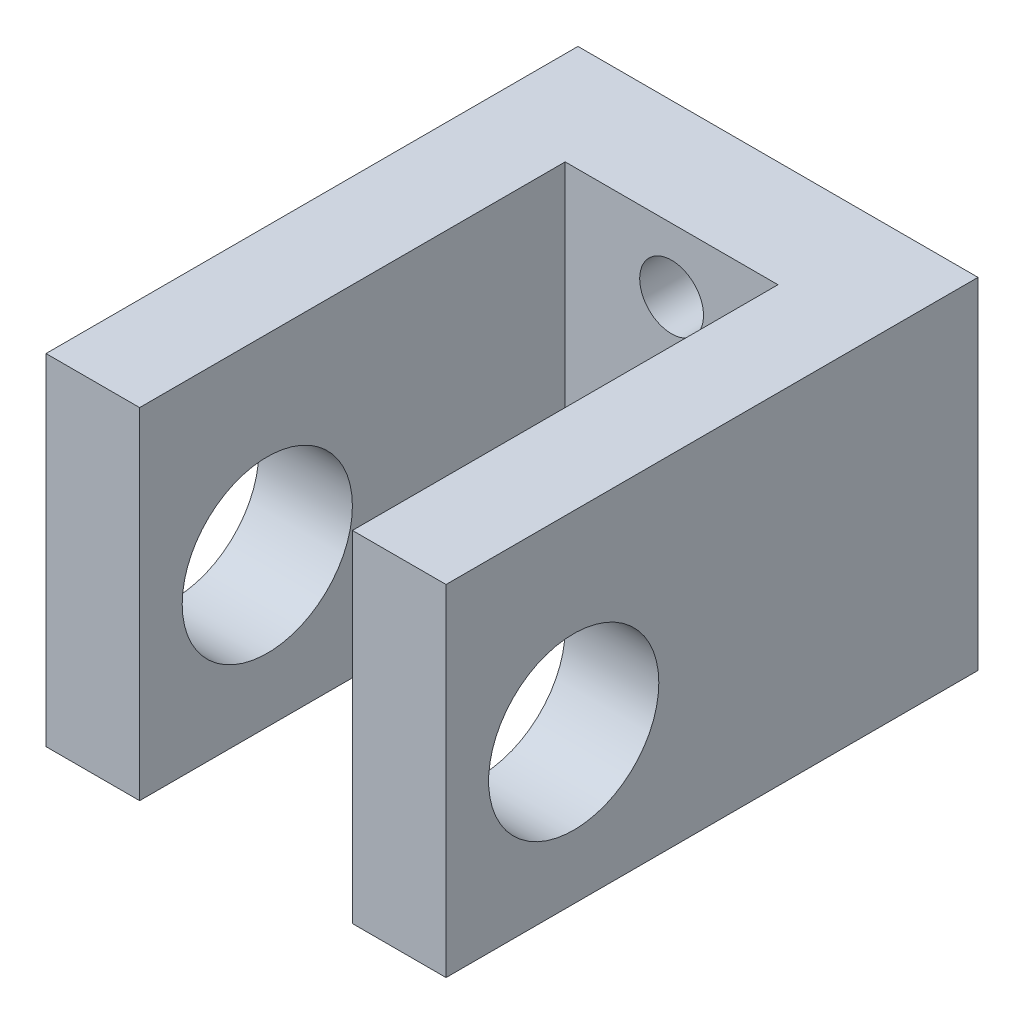
SolidWorks part; units mm, degrees
ref_plane "Front Plane" through (0, 0, 0) normal (0, 0, 1) x (1, 0, 0)
ref_plane "Top Plane" through (0, 0, 0) normal (0, 1, 0) x (1, 0, 0)
ref_plane "Right Plane" through (0, 0, 0) normal (1, 0, 0) x (0, 0, -1)
sketch "Sketch1" plane through (0, 0, 0) normal (0, 1, 0) x (1, 0, 0)
  line L0 (-9.4, 0) -> (9.4, 0) construction
  line L1 (0, 0) -> (0, -11.5565) construction
  line L2 (-9.4, 0) -> (9.4, 0)
  line L3 (9.4, 0) -> (9.4, -25)
  line L4 (9.4, -25) -> (5, -25)
  line L5 (5, -25) -> (5, -5)
  line L6 (5, -5) -> (-5, -5)
  line L7 (-5, -25) -> (-5, -5)
  line L8 (-9.4, -25) -> (-5, -25)
  line L9 (-9.4, 0) -> (-9.4, -25)
  point P10 (0, -5)
  dimension "D1" = 25
  dimension "D2" = 4.4
  dimension "D3" = 9.4
  dimension "D4" = 5
extrude "Boss-Extrude1" add sketch "Sketch1" along normal blind 16
sketch "Sketch2" plane through (9.4, 0, 0) normal (1, 0, 0) x (0, 0, -1)
  line L0 (-25, 16) -> (-25, 0) construction
  line L1 (-25, 0) -> (0, 0) construction
  circle A0 centre (-19, 7) radius 4
  dimension "D1" = 8
  dimension "D2" = 6
  dimension "D3" = 7
extrude "Cut-Extrude1" cut sketch "Sketch2" against normal through all
sketch "Sketch3" plane through (0, 0, 0) normal (0, 0, -1) x (-1, 0, 0)
  line L0 (0, 16) -> (0, 0) construction
  line L1 (-9.4, 16) -> (9.4, 16) construction
  line L2 (-9.4, 0) -> (9.4, 0) construction
  line L3 (-9.4, 8) -> (9.4, 8) construction
  line L4 (-9.4, 16) -> (-9.4, 0) construction
  line L5 (9.4, 16) -> (9.4, 0) construction
  circle A0 centre (0, 13) radius 1.5
  circle A1 centre (0, 3) radius 1.5
  dimension "D1" = 3
  dimension "D2" = 5
extrude "Cut-Extrude2" cut sketch "Sketch3" against normal through all
